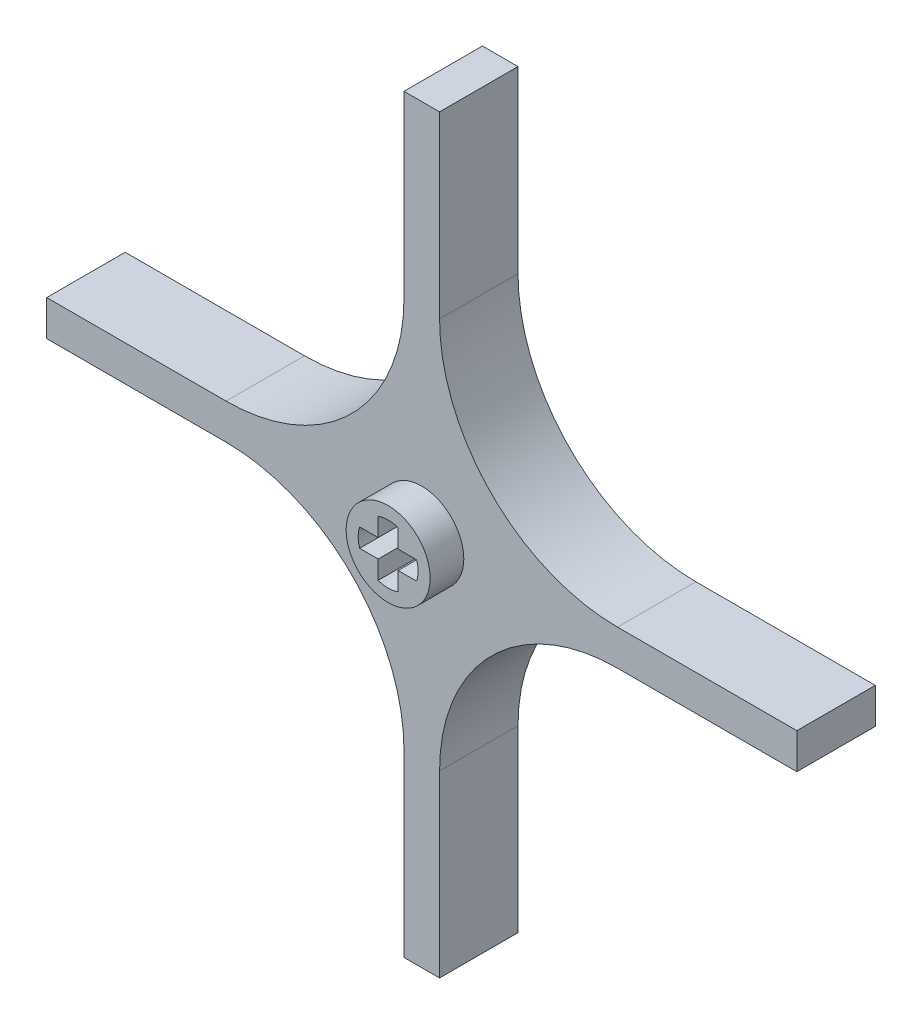
SolidWorks part; units mm, degrees
ref_plane "Front Plane" through (0, 0, 0) normal (0, 0, 1) x (1, 0, 0)
ref_plane "Top Plane" through (0, 0, 0) normal (0, 1, 0) x (1, 0, 0)
ref_plane "Right Plane" through (0, 0, 0) normal (1, 0, 0) x (0, 0, -1)
sketch "Sketch1" plane through (0, 0, 0) normal (0, 0, 1) x (1, 0, 0)
  line L0 (1.5875, -1.5875) -> (1.5875, -33.4645)
  line L1 (-1.5875, 33.4645) -> (1.5875, 33.4645)
  line L2 (-1.5875, 33.4645) -> (-1.5875, 1.5875)
  line L3 (-1.5875, -33.4645) -> (1.5875, -33.4645)
  line L4 (1.5875, 33.4645) -> (1.5875, 1.5875)
  line L5 (-1.5875, 33.4645) -> (1.5875, -33.4645) construction
  line L6 (-1.5875, -33.4645) -> (1.5875, 33.4645) construction
  line L7 (-33.4645, 1.5875) -> (-1.5875, 1.5875)
  line L8 (-33.4645, 1.5875) -> (-33.4645, -1.5875)
  line L9 (-33.4645, -1.5875) -> (-1.5875, -1.5875)
  line L10 (33.4645, 1.5875) -> (33.4645, -1.5875)
  line L11 (-33.4645, 1.5875) -> (33.4645, -1.5875) construction
  line L12 (-33.4645, -1.5875) -> (33.4645, 1.5875) construction
  line L13 (1.5875, -1.5875) -> (33.4645, -1.5875)
  line L14 (1.5875, 1.5875) -> (33.4645, 1.5875)
  line L15 (-1.5875, -1.5875) -> (-1.5875, -33.4645)
  circle A0 centre (17.526, 17.526) radius 15.9385 construction
  circle A1 centre (0, 0) radius 42.8625 construction
  point P0 (0, 0)
  point P6 (0, 0)
  dimension "D3" = 31.877
  dimension "D4" = 85.725
  dimension "D1" = 3.175
  dimension "D2" = 3.175
extrude "Boss-Extrude1" add sketch "Sketch1" along normal mid plane 7 contours L7 L2 L1 L4 L14 L10 L13 L0 L3 L15 L9 L8
fillet "Fillet1" radius 15.875 4 edges at (-1.5875, -1.5875, 0) (-1.5875, 1.5875, 0) (1.5875, -1.5875, 0) (1.5875, 1.5875, 0)
sketch "Sketch2" plane through (0, 0, 3.5) normal (0, 0, 1) x (1, 0, 0)
  circle A0 centre (0, 0) radius 42.8625
sketch "Sketch3" plane through (0, 0, -3.5) normal (0, 0, -1) x (-1, 0, 0)
  circle A0 centre (0, 0) radius 3.75
  dimension "D1" = 7.5
extrude "Boss-Extrude2" add sketch "Sketch3" along normal blind 3 and the other way blind 10
sketch "Sketch4" plane through (0, 0, -6.5) normal (0, 0, -1) x (-1, 0, 0)
  line L0 (-0.889, 0.8255) -> (-0.889, 2.4765)
  line L1 (0.889, 2.4765) -> (0.889, 0.8255)
  line L2 (-0.889, 0.8255) -> (0.889, 0.8255) construction
  line L3 (-0.889, 0.8255) -> (-0.889, -0.8255) construction
  line L4 (-0.889, 0.8255) -> (-2.54, 0.8255)
  line L5 (-2.54, -0.8255) -> (-0.889, -0.8255)
  line L6 (-0.889, -0.8255) -> (-0.889, -2.4765)
  line L7 (0.889, -2.4765) -> (0.889, -0.8255)
  line L8 (0.889, -0.8255) -> (2.54, -0.8255)
  line L9 (0.889, 0.8255) -> (2.54, 0.8255)
  line L10 (2.54, 0.8255) -> (0.889, 0.8255)
  circle A0 centre (0, 0) radius 2.5157 construction
  arc A1 (-0.889, 2.4765) -> (0.889, 2.4765) centre (0, 0.0332) cw
  arc A2 (-2.54, 0.8255) -> (-2.54, -0.8255) centre (-0.0745, 0) ccw
  arc A3 (-0.889, -2.4765) -> (0.889, -2.4765) centre (0, -0.0332) ccw
  arc A4 (2.54, 0.8255) -> (2.54, -0.8255) centre (0.0745, 0) cw
  point P6 (0, 0.8255)
  point P20 (-2.6745, 0)
  point P21 (0, -2.6332)
  point P22 (-0.889, -0.8255)
  point P24 (0.8112, 0.8255)
  dimension "D3" = 2.6
  dimension "D1" = 1.651
  dimension "D2" = 1.778
extrude "Cut-Extrude1" cut sketch "Sketch4" against normal through all
